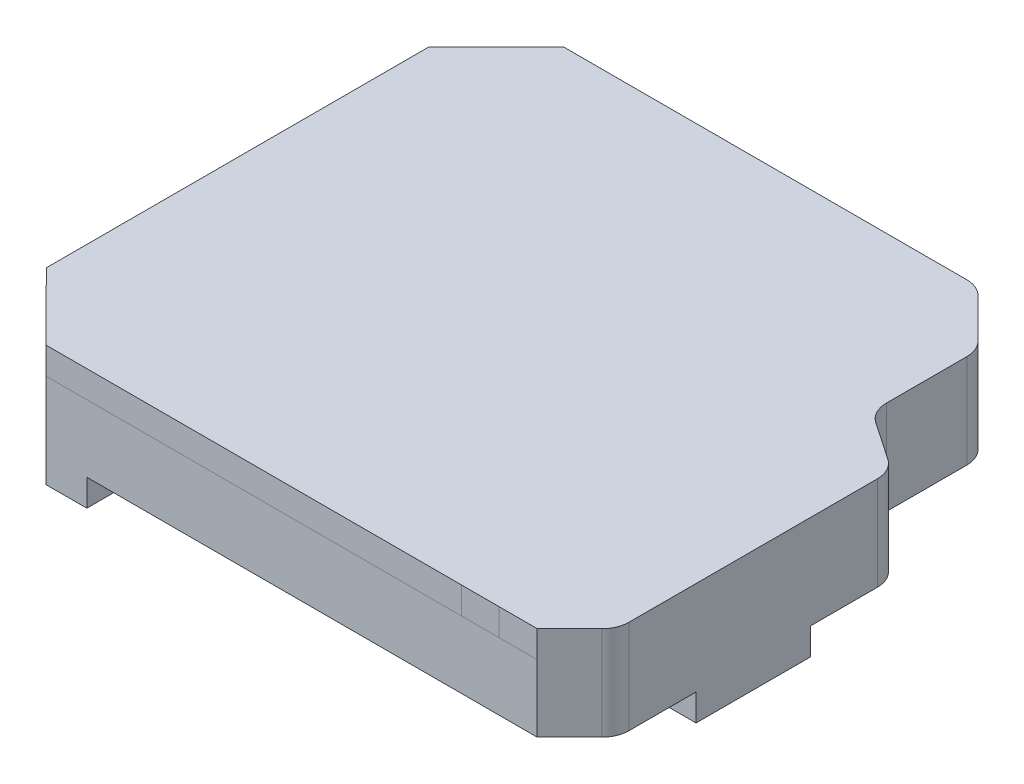
SolidWorks part; units mm, degrees
ref_plane "Front Plane" through (0, 0, 0) normal (0, 0, 1) x (1, 0, 0)
ref_plane "Top Plane" through (0, 0, 0) normal (0, 1, 0) x (1, 0, 0)
ref_plane "Right Plane" through (0, 0, 0) normal (1, 0, 0) x (0, 0, -1)
sketch "Sketch1" plane through (0, 0, 0) normal (0, 1, 0) x (1, 0, 0)
  line L0 (-34.6415, 17.5848) -> (-34.6415, -16.9152)
  line L1 (-31.6415, 14.5848) -> (3.3585, 14.5848)
  line L2 (-31.6415, 14.5848) -> (-31.6415, -13.9152)
  line L3 (-31.6415, -13.9152) -> (3.3585, -13.9152)
  line L4 (3.3585, 14.5848) -> (3.3585, -13.9152)
  line L5 (-34.6415, -16.9152) -> (6.3585, -16.9152)
  line L6 (6.3585, 17.5848) -> (6.3585, -16.9152)
  line L7 (-34.6415, 17.5848) -> (6.3585, 17.5848)
  dimension "D1" = 3
extrude "Boss-Extrude1" add sketch "Sketch1" along normal blind 5
sketch "Sketch2" plane through (0, 0, 0) normal (0, 1, 0) x (1, 0, 0)
  line L1 (-31.6415, 14.5848) -> (3.3585, 14.5848)
  line L2 (-31.6415, 14.5848) -> (-31.6415, -13.9152)
  line L3 (-31.6415, -13.9152) -> (3.3585, -13.9152)
  line L4 (3.3585, 14.5848) -> (3.3585, -13.9152)
extrude "Boss-Extrude2" add sketch "Sketch2" along normal blind 1
sketch "Sketch6" plane through (-34.6415, 0, 0) normal (-1, 0, 0) x (0, 0, 1)
  line L1 (-17.5848, 5) -> (16.9152, 5)
  line L2 (-17.5848, 5) -> (-17.5848, 0)
  line L3 (-17.5848, 0) -> (16.9152, 0)
  line L4 (16.9152, 5) -> (16.9152, 0)
extrude "Cut-Extrude2" cut sketch "Sketch6" against normal blind 3
sketch "Sketch7" plane through (0, 1, 0) normal (0, 1, 0) x (1, 0, 0)
  line L1 (-31.6415, 14.5848) -> (-30.0415, 14.5848)
  line L2 (-31.6415, 14.5848) -> (-31.6415, 11.5848)
  line L3 (-31.6415, 11.5848) -> (-30.0415, 11.5848)
  line L4 (-30.0415, 14.5848) -> (-30.0415, 11.5848)
  line L5 (-31.6415, -13.9152) -> (-30.0415, -13.9152)
  line L6 (-31.6415, -13.9152) -> (-31.6415, -10.8365)
  line L7 (-31.6415, -10.8365) -> (-30.0415, -10.8365)
  line L8 (-30.0415, -13.9152) -> (-30.0415, -10.8365)
extrude "Boss-Extrude3" add sketch "Sketch7" along normal blind 4
chamfer "Chamfer1" distance 3 angle 45 4 edges at (6.3585, 2.5, -17.5848) (6.3585, 2.5, 16.9152) (-31.6415, 2.5, -17.5848) (-31.6415, 2.5, 16.9152)
sketch "Sketch14" plane through (0, 1, 0) normal (0, 1, 0) x (1, 0, 0)
  line L0 (167.1391, 423.2739) -> (1080.46, 418.4917) construction
  line L1 (3.3585, -13.9152) -> (3.3585, 14.5848) construction
  line L2 (3.3585, 3.0917) -> (6.8611, 3.0917)
  line L3 (3.3585, 3.0917) -> (3.3585, -17.3608)
  line L4 (3.3585, -17.3608) -> (6.8611, -17.3608)
  line L5 (6.8611, 3.0917) -> (6.8611, -17.3608)
extrude "Cut-Extrude6" cut sketch "Sketch14" along normal blind 10
sketch "Sketch17" plane through (0, 1, 0) normal (0, 1, 0) x (1, 0, 0)
  line L0 (3.3585, 3.0917) -> (7.91, 0)
  line L2 (10.91, 3.4196) -> (10.91, -16.9152)
  line L4 (7.91, 0) -> (7.91, -13.9152)
  line L5 (3.3585, -13.9152) -> (7.91, -13.9152)
  line L6 (3.3585, -13.9152) -> (3.3585, -16.9152)
  line L7 (3.3585, -16.9152) -> (10.91, -16.9152)
  line L9 (10.91, 3.4196) -> (3.3585, 8.5491)
  line L10 (3.3585, 3.0917) -> (3.3585, 14.5848) construction
  line L11 (3.3585, 8.5491) -> (3.3585, 3.0917)
extrude "Boss-Extrude5" add sketch "Sketch17" along normal blind 4
sketch "Sketch19" plane through (0, 0, 0) normal (0, -1, 0) x (1, 0, 0)
  line L0 (3.3585, 16.9152) -> (10.91, 16.9152)
  line L1 (10.91, 16.9152) -> (10.91, -3.4196)
  line L2 (10.91, -3.4196) -> (6.3585, -6.5113)
  line L3 (6.3585, -6.5113) -> (6.3585, 13.9152)
  line L4 (6.3585, 13.9152) -> (3.3585, 16.9152)
extrude "Boss-Extrude7" add sketch "Sketch19" against normal blind 1
sketch "Sketch9" plane through (0, 1, 0) normal (0, 1, 0) x (1, 0, 0)
  line L1 (-31.6415, 11.5848) -> (-28.3587, 11.5848)
  line L2 (-31.6415, 11.5848) -> (-31.6415, -10.8359)
  line L3 (-31.6415, -10.8359) -> (-28.3587, -10.8359)
  line L4 (-28.3587, 11.5848) -> (-28.3587, -10.8359)
extrude "Cut-Extrude3" cut sketch "Sketch9" against normal blind 4
sketch "Sketch11" plane through (0, 0, 0) normal (0, -1, 0) x (1, 0, 0)
  line L0 (-26.6655, 18.9152) -> (-31.6415, 13.9152)
  line L1 (-31.6415, 13.9152) -> (-31.6415, -14.5848)
  line L2 (-31.6415, -14.5848) -> (-26.6292, -19.5848)
  line L3 (-26.6292, -19.5848) -> (4.2338, -19.5848)
  line L4 (4.2338, -19.5848) -> (8.3585, -15.4601)
  line L5 (8.3585, -15.4601) -> (8.3585, 14.7437)
  line L6 (8.3585, 14.7437) -> (4.264, 18.9152)
  line L7 (4.264, 18.9152) -> (-26.6655, 18.9152)
extrude "Boss-Extrude4" add sketch "Sketch11" along normal blind 2
sketch "Sketch12" plane through (0, 0, 0) normal (0, 1, 0) x (1, 0, 0)
  line L1 (-28.3587, 11.5848) -> (-31.6415, 11.5848)
  line L2 (-28.3587, 11.5848) -> (-28.3587, -10.8359)
  line L3 (-28.3587, -10.8359) -> (-31.6415, -10.8359)
  line L4 (-31.6415, 11.5848) -> (-31.6415, -10.8359)
extrude "Cut-Extrude4" cut sketch "Sketch12" against normal blind 0.0039
sketch "Sketch20" plane through (0, 0, 0) normal (0, -1, 0) x (1, 0, 0)
  line L0 (6.227, 16.9152) -> (10.91, 16.9152)
  line L1 (10.91, 16.9152) -> (10.91, -3.4196)
  line L2 (10.91, -3.4196) -> (8.3585, -5.1528)
  line L3 (8.3585, -5.1528) -> (8.3585, 14.7437)
  line L4 (8.3585, 14.7437) -> (6.227, 16.9152)
extrude "Boss-Extrude8" add sketch "Sketch20" along normal blind 2
sketch "Sketch21" plane through (0, 0, 0) normal (0, 1, 0) x (1, 0, 0)
  line L0 (6.3585, 6.5113) -> (10.9077, 3.4212)
  line L1 (10.9077, 3.4212) -> (10.9077, -16.9128)
  line L2 (10.9077, -16.9128) -> (6.227, -16.9152)
  line L3 (6.227, -16.9152) -> (4.264, -18.9152)
  line L4 (7.4822, 8.1657) -> (12.9077, 4.4804)
  line L5 (12.9077, 4.4804) -> (12.9077, -18.9117)
  line L6 (12.9077, -18.9117) -> (7.0668, -18.9148)
  line L7 (7.0668, -18.9148) -> (5.6913, -20.3162)
  line L8 (7.0668, -18.9148) -> (4.264, -18.9152)
  line L9 (8.3585, 7.5705) -> (8.3585, 5.1528)
  line L10 (8.3585, 15.4601) -> (8.3585, 5.1528) construction
  line M10 (8.3585, 5.1528) -> (8.3585, 15.4601)
  dimension "D1" = 2
extrude "Boss-Extrude9" add sketch "Sketch21" against normal blind 2 contours L8 L6 L5 L4 L0 L1 L2 L3 M10
sketch "Sketch22" plane through (0, 1, 0) normal (0, 1, 0) x (1, 0, 0)
  line L0 (167.2956, 423.4871) -> (1080.6164, 418.7049) construction
sketch "Sketch23" plane through (0, 5, 0) normal (0, 1, 0) x (1, 0, 0)
  line L1 (9.2243, 0.938) -> (-3.3619, 9.4687)
  line L2 (9.2243, 0.938) -> (4.6728, 4.0297)
  line L3 (9.2243, 0.938) -> (4.6728, 4.0297)
  line L4 (-3.3619, 9.4687) -> (16.5933, -4.0566)
  line L5 (7.91, -4.2447) -> (7.91, 10.1169)
  line L6 (7.91, 0) -> (7.91, -13.9152) construction
  line L7 (3.3585, 4.9137) -> (3.3585, 3.0917)
  line L8 (3.3585, 3.0917) -> (7.91, 0)
  line L9 (7.91, 0) -> (7.91, 1.8288)
  line L10 (7.91, 1.8288) -> (3.3585, 4.9137)
  line M11 (3.3585, 14.5848) -> (3.3585, 3.0917)
  line M12 (3.3585, 3.0917) -> (7.91, 0)
  dimension "D1" = 3
extrude "Cut-Extrude7" cut sketch "Sketch23" against normal blind 4 and the other way through all contours L5 L4 M12 M11
chamfer "Chamfer2" distance 3 angle 45 2 edges at (12.9077, -1, 18.9117) (10.91, 2.5, 16.9152)
chamfer "Chamfer3" distance 2 angle 45 1 edges at (7.91, 3, 13.9152)
sketch "Sketch25" plane through (0, 0, 0) normal (0, 1, 0) x (1, 0, 0)
  line L0 (-28.6415, 17.5848) -> (-26.6292, 19.5848)
  line L1 (-26.6292, 19.5848) -> (4.2338, 19.5848)
  line L2 (4.2338, 19.5848) -> (8.3585, 15.4601)
  line L3 (8.3585, 15.4601) -> (8.3585, 7.5705)
  line L4 (8.3585, 7.5705) -> (12.9077, 4.4804)
  line L5 (12.9077, 4.4804) -> (12.9077, -15.9117)
  line L6 (12.9077, -15.9117) -> (9.9061, -18.9133)
  line L7 (9.9061, -18.9133) -> (-26.6655, -18.9152)
  line L8 (-26.6655, -18.9152) -> (-28.6415, -16.9152)
  line L9 (-28.6415, -16.9152) -> (7.91, -16.9152)
  line L10 (7.91, -16.9152) -> (10.91, -13.9152)
  line L11 (10.91, -13.9152) -> (10.91, 3.4196)
  line L12 (10.91, 3.4196) -> (6.3585, 6.5113)
  line L13 (6.3585, 6.5113) -> (6.3585, 14.5848)
  line L14 (6.3585, 14.5848) -> (3.3585, 17.5848)
  line L15 (3.3585, 17.5848) -> (-28.6415, 17.5848)
extrude "Boss-Extrude10" add sketch "Sketch25" along normal blind 7
sketch "Sketch26" plane through (0, -2, 0) normal (0, -1, 0) x (1, 0, 0)
  line L24 (10.9077, -3.4212) -> (10.9077, 15.0833)
  line L25 (10.9077, 15.0833) -> (9.0772, 16.9137)
  line L26 (9.0772, 16.9137) -> (7.0661, 16.9148)
  line L27 (7.0661, 16.9148) -> (4.2638, 16.9152)
  line L28 (4.2638, 16.9152) -> (-25.8343, 16.9152)
  line L29 (-25.8343, 16.9152) -> (-29.6415, 13.0896)
  line L30 (-29.6415, 13.0896) -> (-29.6415, -13.7549)
  line L31 (-29.6415, -13.7549) -> (-25.8022, -17.5848)
  line L32 (-25.8022, -17.5848) -> (3.4054, -17.5848)
  line L33 (3.4054, -17.5848) -> (6.3585, -14.6317)
  line L34 (6.3585, -14.6317) -> (6.3585, -6.5113)
  line L35 (6.3585, -6.5113) -> (10.9077, -3.4212)
  line L36 (10.9077, -3.4212) -> (10.9077, 15.0833)
  line L37 (10.9077, 15.0833) -> (9.0772, 16.9137)
  line L38 (9.0772, 16.9137) -> (7.0661, 16.9148)
  line L39 (7.0661, 16.9148) -> (4.2638, 16.9152)
  line L40 (4.2638, 16.9152) -> (-25.8343, 16.9152)
  line L41 (-25.8343, 16.9152) -> (-29.6415, 13.0896)
  line L42 (-29.6415, 13.0896) -> (-29.6415, -13.7549)
  line L43 (-29.6415, -13.7549) -> (-25.8022, -17.5848)
  line L44 (-25.8022, -17.5848) -> (3.4054, -17.5848)
  line L45 (3.4054, -17.5848) -> (6.3585, -14.6317)
  line L46 (6.3585, -14.6317) -> (6.3585, -6.5113)
  line L47 (6.3585, -6.5113) -> (10.9077, -3.4212)
  dimension "D1" = 2
extrude "Cut-Extrude8" cut sketch "Sketch26" against normal blind 7 from offset 2 offset against normal yes
sketch "Sketch27" plane through (0, 0, 0) normal (0, 1, 0) x (1, 0, 0)
  line L0 (-25.8022, 17.5848) -> (-28.6415, 17.5848)
  line L1 (-28.6415, 17.5848) -> (-31.6415, 14.5848)
  line L2 (-31.6415, 14.5848) -> (-31.6415, 11.5848)
  line L3 (-31.6415, 11.5848) -> (-29.6415, 11.5848)
  line L4 (-29.6415, 11.5848) -> (-29.6415, 13.7549)
  line L5 (-29.6415, 13.7549) -> (-25.8022, 17.5848)
  line L6 (-29.6415, -10.8359) -> (-29.6415, -13.0896)
  line L7 (-29.6415, -13.0896) -> (-25.8343, -16.9152)
  line L8 (-25.8343, -16.9152) -> (-28.6415, -16.9152)
  line L9 (-28.6415, -16.9152) -> (-31.6415, -13.9152)
  line L10 (-31.6415, -13.9152) -> (-31.6415, -10.8359)
  line L11 (-31.6415, -10.8359) -> (-29.6415, -10.8359)
extrude "Cut-Extrude9" cut sketch "Sketch27" along normal blind 7
sketch "Sketch28" plane through (0, -0.0039, 0) normal (0, 1, 0) x (1, 0, 0)
  line L1 (-31.6415, -13.9152) -> (-26.6655, -18.9152)
  line L2 (-26.6655, -18.9152) -> (9.9061, -18.9133)
  line L3 (9.9061, -18.9133) -> (12.9077, -15.9117)
  line L4 (12.9077, -15.9117) -> (12.9077, 4.4804)
  line L5 (12.9077, 4.4804) -> (8.3585, 7.5705)
  line L6 (8.3585, 7.5705) -> (8.3585, 15.4601)
  line L7 (8.3585, 15.4601) -> (4.2338, 19.5848)
  line L8 (4.2338, 19.5848) -> (-26.6292, 19.5848)
  line L9 (-26.6292, 19.5848) -> (-31.6415, 14.5848)
  line L10 (-31.6415, 14.5848) -> (-31.6415, -13.9152)
extrude "Cut-Extrude11" cut sketch "Sketch28" along normal blind 10 from offset 1
sketch "Sketch29" plane through (0, -0.0039, 0) normal (0, 1, 0) x (1, 0, 0)
  line L0 (-31.6415, 14.5848) -> (-26.6292, 19.5848)
  line L1 (-26.6292, 19.5848) -> (4.2338, 19.5848)
  line L2 (4.2338, 19.5848) -> (8.3585, 15.4601)
  line L3 (8.3585, 15.4601) -> (8.3585, 7.5705)
  line L4 (8.3585, 7.5705) -> (12.9077, 4.4804)
  line L5 (12.9077, 4.4804) -> (12.9077, -15.9117)
  line L6 (12.9077, -15.9117) -> (9.9061, -18.9133)
  line L7 (9.9061, -18.9133) -> (-26.6655, -18.9152)
  line L8 (-26.6655, -18.9152) -> (-31.6415, -13.9152)
  line L9 (-31.6415, -13.9152) -> (-31.6415, 14.5848)
extrude "Cut-Extrude12" cut sketch "Sketch29" along normal blind 10
sketch "Sketch30" plane through (-23.0248, 0, -23.1671) normal (-0.7049, 0, -0.7093) x (-0.7093, 0, 0.7049)
  line L1 (5.0818, 7) -> (7.919, 7)
  line L2 (5.0818, 7) -> (5.0818, 0)
  line L3 (5.0818, 0) -> (7.919, 0)
  line L4 (7.919, 7) -> (7.919, 0)
extrude "Cut-Extrude13" cut sketch "Sketch30" against normal blind 10
sketch "Sketch31" plane through (0, -2, 0) normal (0, -1, 0) x (1, 0, 0)
  line L0 (-26.6655, 18.9152) -> (-31.6415, 13.9152)
  line L1 (-31.6415, 13.9152) -> (-29.6415, 13.0896)
  line L2 (-26.6655, 18.9152) -> (9.9061, 18.9133)
  line L3 (9.9061, 18.9133) -> (12.9077, 15.9117)
  line L4 (12.9077, 15.9117) -> (12.9077, -4.4804)
  line L5 (12.9077, -4.4804) -> (8.3585, -7.5705)
  line L6 (8.3585, -7.5705) -> (8.3585, -15.4601)
  line L7 (8.3585, -15.4601) -> (4.2338, -19.5848)
  line L8 (4.2338, -19.5848) -> (-26.6292, -19.5848)
  line L9 (-26.6292, -19.5848) -> (-31.6415, -14.5848)
  line L10 (-31.6415, -14.5848) -> (-31.6415, 13.9152)
  line L11 (-29.6415, -13.7549) -> (-31.6415, -14.5848)
  line L24 (10.9077, -3.4212) -> (10.9077, 15.0833)
  line L25 (10.9077, 15.0833) -> (9.0772, 16.9137)
  line L26 (9.0772, 16.9137) -> (7.0661, 16.9148)
  line L27 (7.0661, 16.9148) -> (4.2638, 16.9152)
  line L28 (4.2638, 16.9152) -> (-25.8343, 16.9152)
  line L29 (-25.8343, 16.9152) -> (-29.6415, 13.0896)
  line L30 (-29.6415, 13.0896) -> (-29.6415, -13.7549)
  line L31 (-29.6415, -13.7549) -> (-25.8022, -17.5848)
  line L32 (-25.8022, -17.5848) -> (3.4054, -17.5848)
  line L33 (3.4054, -17.5848) -> (6.3585, -14.6317)
  line L34 (6.3585, -14.6317) -> (6.3585, -6.5113)
  line L35 (6.3585, -6.5113) -> (10.9077, -3.4212)
  line L36 (10.9077, -3.4212) -> (10.9077, 15.0833)
  line L37 (10.9077, 15.0833) -> (9.0772, 16.9137)
  line L38 (9.0772, 16.9137) -> (7.0661, 16.9148)
  line L39 (7.0661, 16.9148) -> (4.2638, 16.9152)
  line L40 (4.2638, 16.9152) -> (-25.8343, 16.9152)
  line L41 (-25.8343, 16.9152) -> (-29.6415, 13.0896)
  line L42 (-29.6415, 13.0896) -> (-29.6415, -13.7549)
  line L43 (-29.6415, -13.7549) -> (-25.8022, -17.5848)
  line L44 (-25.8022, -17.5848) -> (3.4054, -17.5848)
  line L45 (3.4054, -17.5848) -> (6.3585, -14.6317)
  line L46 (6.3585, -14.6317) -> (6.3585, -6.5113)
  line L47 (6.3585, -6.5113) -> (10.9077, -3.4212)
  line M13 (12.9077, -4.4804) -> (12.9077, 15.9117)
  line M14 (12.9077, 15.9117) -> (9.9061, 18.9133)
  line M18 (-26.6655, 18.9152) -> (-31.6415, 13.9152)
  line M20 (-31.6415, -14.5848) -> (-26.6292, -19.5848)
  line M21 (-26.6292, -19.5848) -> (4.2338, -19.5848)
  line M22 (4.2338, -19.5848) -> (8.3585, -15.4601)
  line M23 (8.3585, -15.4601) -> (8.3585, -7.5705)
  line M24 (8.3585, -7.5705) -> (12.9077, -4.4804)
  dimension "D1" = 2
extrude "Boss-Extrude11" add sketch "Sketch31" along normal blind 7 contours L47 L46 L45 L44 L43 L11 L2 L1 L41 L40 L39 L38 L37 L36 M20 M21 M22 M23 M24 M13 M14 M18
sketch "Sketch32" plane through (0, -2, 0) normal (0, -1, 0) x (1, 0, 0)
  line L0 (-25.8343, 16.9152) -> (-36.8448, 16.9152)
  line L1 (-36.8448, 16.9152) -> (-37.657, -20.4953)
  line L2 (-25.8022, -17.5848) -> (-37.5938, -17.5848)
  line L3 (-25.8343, 16.9152) -> (-25.8022, -17.5848)
  line M1 (-29.6415, 13.0896) -> (-31.6415, 13.9152)
  line M2 (-31.6415, 13.9152) -> (-31.6415, -14.5848)
  line M3 (-31.6415, -14.5848) -> (-29.6415, -13.7549)
  line M4 (-29.6415, -13.7549) -> (-25.8022, -17.5848)
  line M14 (-25.8343, 16.9152) -> (-29.6415, 13.0896)
extrude "Cut-Extrude14" cut sketch "Sketch32" along normal blind 7 contours L3 M14 M1 M2 M3 M4 | L2 L0 L1 M4 M3 M2 M1 M14
sketch "Sketch35" plane through (0, -9, 0) normal (0, -1, 0) x (1, 0, 0)
  line L0 (-26.6655, 18.9152) -> (9.9061, 18.9133) construction
  line L1 (-23.6262, 18.9151) -> (13.0196, 18.9151)
  line L2 (-23.6262, 18.9151) -> (-23.6262, -19.5848)
  line L3 (-23.6262, -19.5848) -> (13.0196, -19.5848)
  line L4 (13.0196, 18.9151) -> (13.0196, -19.5848)
extrude "Cut-Extrude15" cut sketch "Sketch35" against normal blind 2
sketch "Sketch37" plane through (0, -7, 0) normal (0, -1, 0) x (1, 0, 0)
  line L0 (10.9077, -3.4212) -> (10.9077, 15.0833) construction
  line L1 (10.9077, 10.0835) -> (12.9077, 10.0835)
  line L2 (10.9077, 10.0835) -> (10.9077, 1.576)
  line L3 (10.9077, 1.576) -> (12.9077, 1.576)
  line L4 (12.9077, 10.0835) -> (12.9077, 1.576)
  line L5 (12.9077, -4.4804) -> (12.9077, 15.9117) construction
extrude "Boss-Extrude12" add sketch "Sketch37" along normal blind 2
fillet "Fillet2" radius 2 5 edges at (8.3585, -3.5019, -7.5705) (8.3585, -3.5019, -15.4601) (4.2338, -3.5019, -19.5848) (12.9077, -3.5019, 15.9117) (12.9077, -3.5019, -4.4804)
